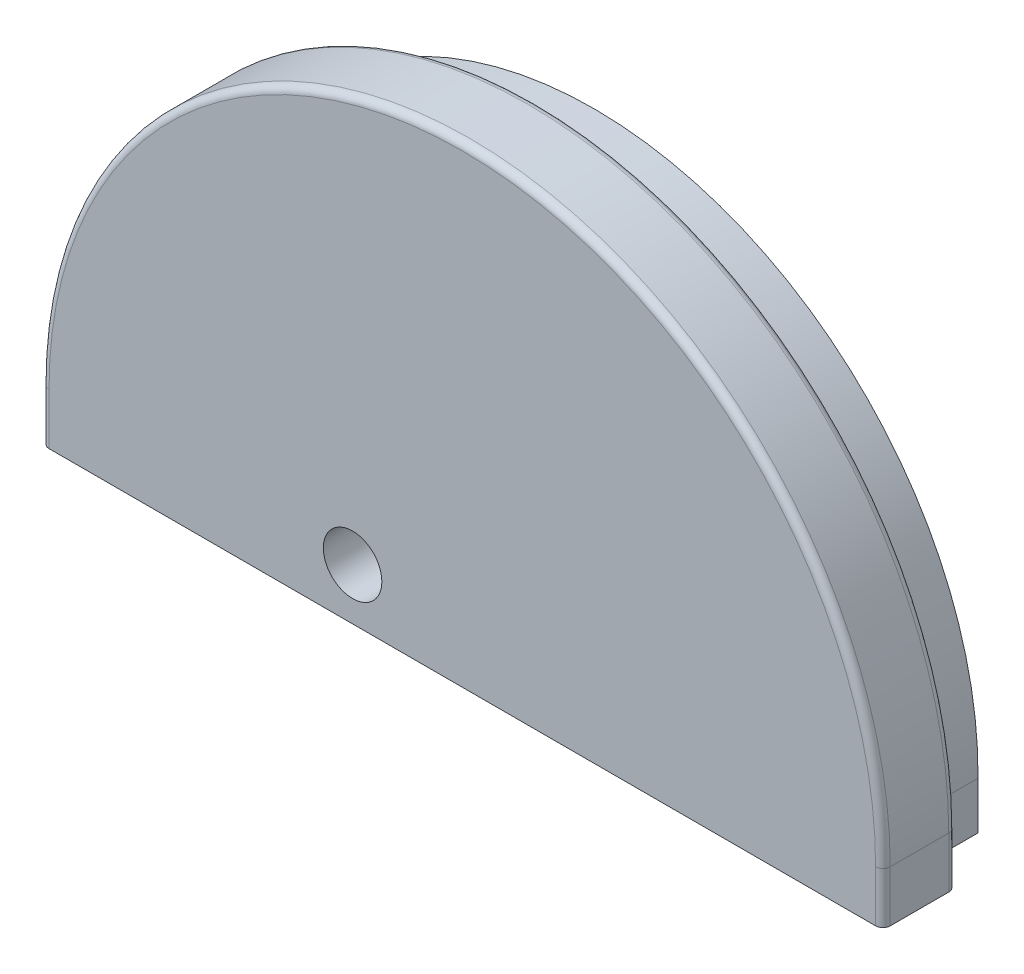
SolidWorks part; units mm, degrees
ref_plane "Front Plane" through (0, 0, 0) normal (0, 0, 1) x (1, 0, 0)
ref_plane "Top Plane" through (0, 0, 0) normal (0, 1, 0) x (1, 0, 0)
ref_plane "Right Plane" through (0, 0, 0) normal (1, 0, 0) x (0, 0, -1)
sketch "Sketch1" plane through (0, 0, 0) normal (0, 0, 1) x (1, 0, 0)
  line L0 (49.7401, 55.7881) -> (49.7401, 48.7881)
  line L2 (49.7401, 48.7881) -> (154.7375, 48.7881)
  line L3 (154.7375, 48.7881) -> (154.7375, 55.2644)
  arc A1 (49.7401, 55.7881) -> (154.7375, 55.2644) centre (102.2401, 55.7881) cw
extrude "Boss-Extrude1" add sketch "Sketch1" along normal blind 8
sketch "Sketch2" plane through (0, 0, 8) normal (0, 0, 1) x (1, 0, 0)
  line L2 (159.7401, 55.7881) -> (159.7401, 48.7881)
  line L3 (159.7401, 48.7881) -> (44.7401, 48.7881)
  line L4 (44.7401, 55.7881) -> (44.7401, 48.7881)
  arc A1 (44.7401, 55.7881) -> (159.7401, 55.7881) centre (102.2401, 55.7881) cw
extrude "Boss-Extrude2" add sketch "Sketch2" along normal blind 10
sketch "Sketch3" plane through (0, 0, 18) normal (0, 0, 1) x (1, 0, 0)
  circle A0 centre (87.2401, 55.7881) radius 4
extrude "Cut-Extrude1" cut sketch "Sketch3" against normal up to body
fillet "Fillet1" radius 1 6 edges at (159.7401, 52.2881, 8) (44.7401, 52.2881, 8) (159.7401, 52.2881, 18) (44.7401, 52.2881, 18) (102.2401, 113.2881, 8) (102.2401, 113.2881, 18)
sketch "Sketch6" plane through (0, 0, 0) normal (0, 0, 1) x (1, 0, 0)
  line L5 (72.3918, 48.7881) -> (57.3918, 48.7881)
  line L7 (72.3918, 58.7547) -> (72.3918, 48.7881)
  line L8 (57.3918, 48.7881) -> (57.3918, 58.7547)
  arc A5 (72.3918, 58.7547) -> (57.3918, 58.7547) centre (64.8918, 58.7547) ccw
extrude "Cut-Extrude3" cut sketch "Sketch6" along normal blind 4.5
fillet "Fillet2" radius 2 6 edges at (72.3918, 53.7714, 0) (57.3918, 53.7714, 0) (57.3918, 53.7714, 4.5) (64.8918, 66.2547, 4.5) (64.8918, 66.2547, 0) (72.3918, 53.7714, 4.5)
